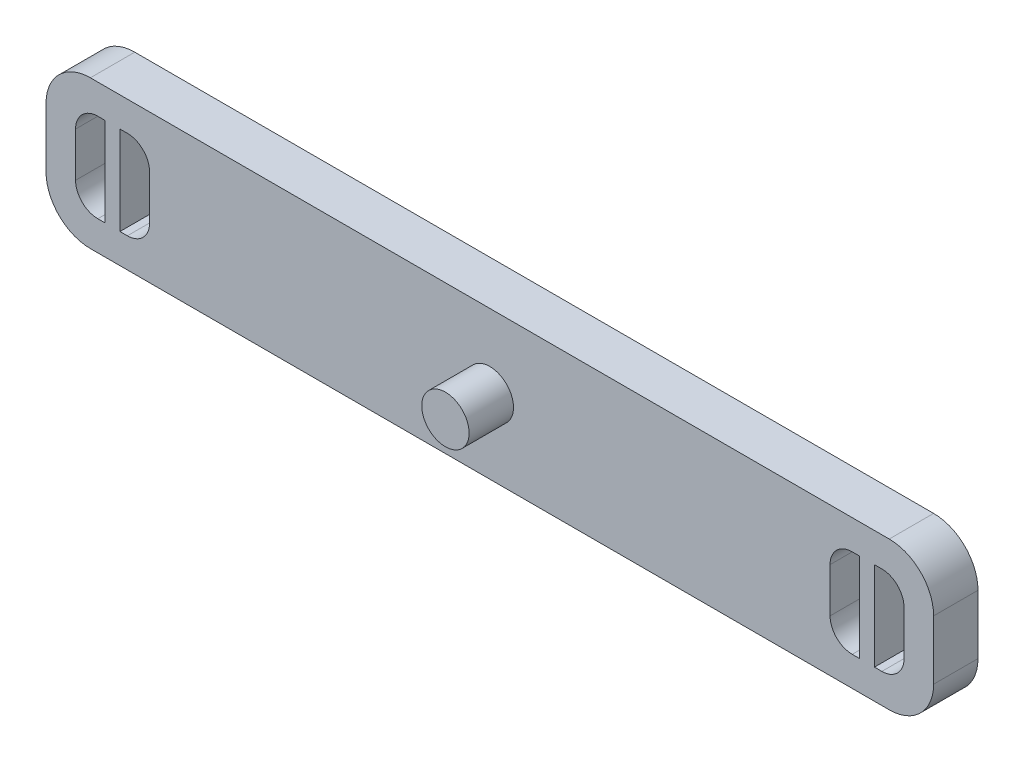
SolidWorks part; units mm, degrees
ref_plane "Front Plane" through (0, 0, 0) normal (0, 0, 1) x (1, 0, 0)
ref_plane "Top Plane" through (0, 0, 0) normal (0, 1, 0) x (1, 0, 0)
ref_plane "Right Plane" through (0, 0, 0) normal (1, 0, 0) x (0, 0, -1)
sketch "Sketch1" plane through (0, 0, 0) normal (0, 0, 1) x (1, 0, 0)
  line L1 (-30, 5) -> (30, 5)
  line L2 (-30, 5) -> (-30, -5)
  line L3 (-30, -5) -> (30, -5)
  line L4 (30, 5) -> (30, -5)
  line L5 (-30, 5) -> (30, -5) construction
  line L6 (-30, -5) -> (30, 5) construction
  point P0 (0, 0)
  dimension "D1" = 60
  dimension "D2" = 10
extrude "Boss-Extrude1" add sketch "Sketch1" along normal blind 3
sketch "Sketch2" plane through (0, 0, 3) normal (0, 0, 1) x (1, 0, 0)
  circle A0 centre (0, 0) radius 1.6
sketch "Sketch3" plane through (0, 0, 3) normal (0, 0, 1) x (1, 0, 0)
  line L0 (-30, 5) -> (-30, -5) construction
  line L1 (-26.5, 3) -> (-26, 3)
  line L2 (-28, 1.5) -> (-28, -1.5)
  line L3 (-26.5, -3) -> (-26, -3)
  line L4 (-26, 3) -> (-26, -3)
  line L5 (-30, -5) -> (30, -5) construction
  line L6 (30, 5) -> (-30, 5) construction
  line L8 (-25, 3) -> (-24.5, 3)
  line L9 (-25, 3) -> (-25, -3)
  line L10 (-25, -3) -> (-24.5, -3)
  line L11 (-23, 1.5) -> (-23, -1.5)
  arc A0 (-24.5, -3) -> (-23, -1.5) centre (-24.5, -1.5) ccw
  arc A1 (-24.5, 3) -> (-23, 1.5) centre (-24.5, 1.5) cw
  arc A2 (-28, -1.5) -> (-26.5, -3) centre (-26.5, -1.5) ccw
  arc A3 (-26.5, 3) -> (-28, 1.5) centre (-26.5, 1.5) ccw
  point P18 (-23, 3)
  point P23 (-28, 3)
  dimension "D7" = 1.5
  dimension "D1" = 2
  dimension "D2" = 2
  dimension "D3" = 2
  dimension "D4" = 2
  dimension "D5" = 1
  dimension "D6" = 2
extrude "Cut-Extrude2" cut sketch "Sketch3" against normal blind 3
mirror "Mirror1" about plane through (0, 0, 0) normal (1, 0, 0) of "Cut-Extrude2"
fillet "Fillet1" radius 3 4 edges at (-30, -5, 1.5) (-30, 5, 1.5) (30, -5, 1.5) (30, 5, 1.5)
extrude "Boss-Extrude2" add sketch "Sketch2" along normal blind 3
